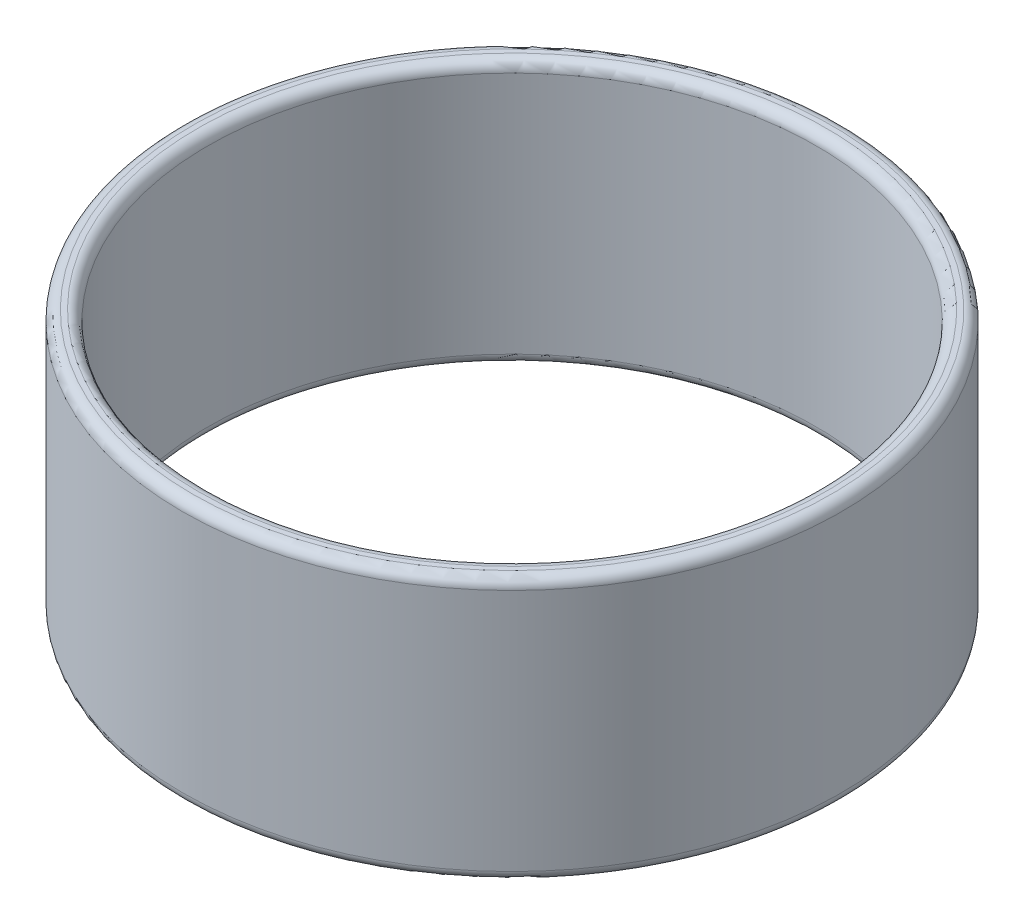
SolidWorks part; units mm, degrees
ref_plane "前视基准面" through (0, 0, 0) normal (0, 0, 1) x (1, 0, 0)
ref_plane "上视基准面" through (0, 0, 0) normal (0, 1, 0) x (1, 0, 0)
ref_plane "右视基准面" through (0, 0, 0) normal (1, 0, 0) x (0, 0, -1)
sketch "草图1" plane through (0, 0, 0) normal (0, 1, 0) x (1, 0, 0)
  circle A0 centre (0, 0) radius 30
  circle A1 centre (0, 0) radius 32.5
  dimension "D1" = 65
  dimension "D2" = 60
extrude "凸台-拉伸1" add sketch "草图1" along normal blind 26
fillet "圆角1" radius 1 4 edges at (0, 0, 30) (0, 0, 32.5) (0, 26, 30) (0, 26, 32.5)
